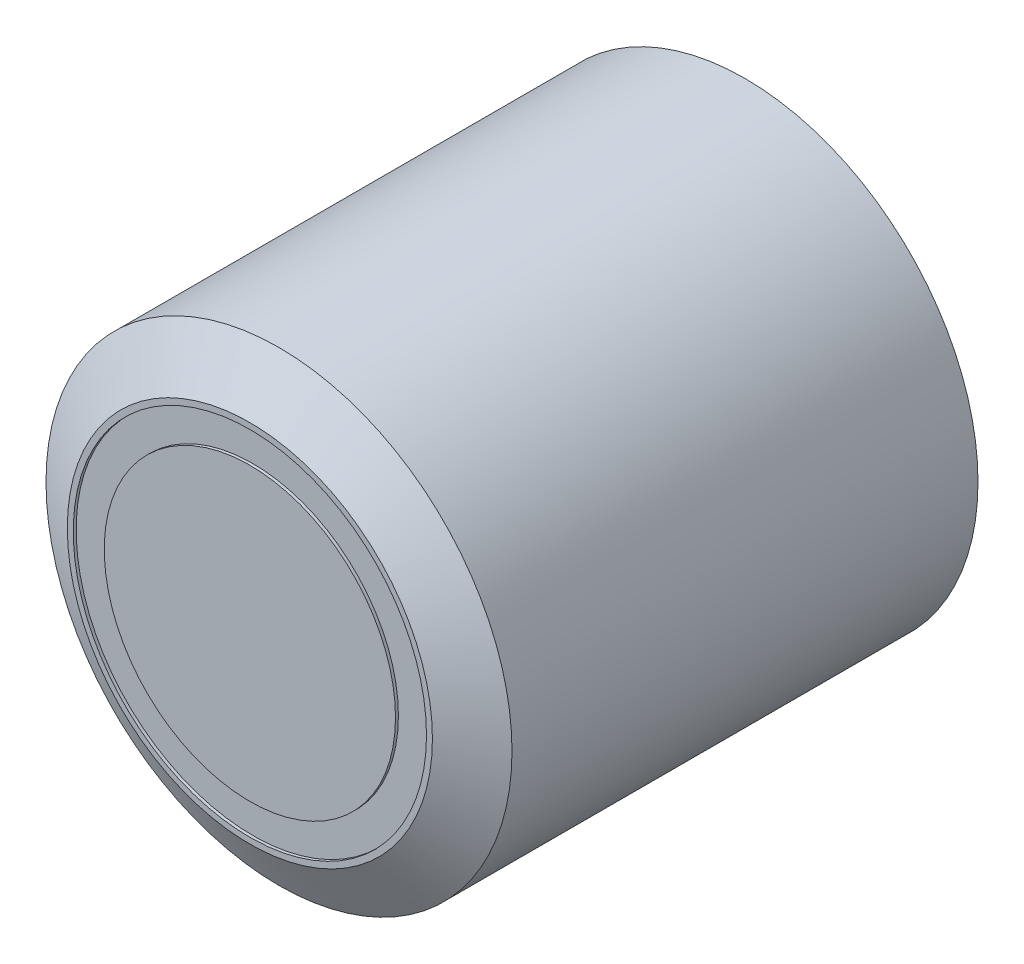
SolidWorks part; units mm, degrees
ref_plane "Front Plane" through (0, 0, 0) normal (0, 0, 1) x (1, 0, 0)
ref_plane "Top Plane" through (0, 0, 0) normal (0, 1, 0) x (1, 0, 0)
ref_plane "Right Plane" through (0, 0, 0) normal (1, 0, 0) x (0, 0, -1)
sketch "Sketch2" plane through (0, 0, 0) normal (0, 0, 1) x (1, 0, 0)
  circle A0 centre (0, 0) radius 8
  dimension "D1" = 16
extrude "Boss-Extrude1" add sketch "Sketch2" along normal blind 17
chamfer "Chamfer1" distance 1 angle 60 1 edges at (8, 0, 17)
sketch "Sketch5" plane through (0, 0, 17) normal (0, 0, 1) x (1, 0, 0)
  circle A0 centre (0, 0) radius 6.0643
extrude "Cut-Extrude1" cut sketch "Sketch5" against normal blind 0.1
sketch "Sketch6" plane through (0, 0, 16.9) normal (0, 0, 1) x (1, 0, 0)
  circle A0 centre (0, 0) radius 5
extrude "Boss-Extrude4" add sketch "Sketch6" along normal blind 0.1
